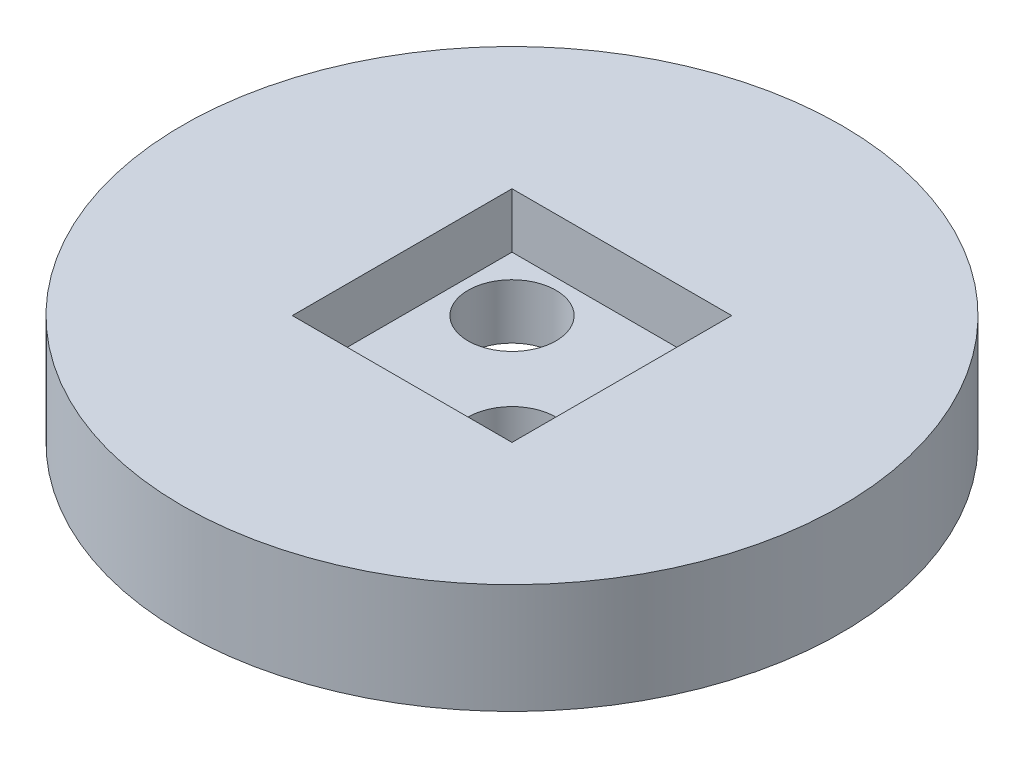
SolidWorks part; units mm, degrees
ref_plane "Front Plane" through (0, 0, 0) normal (0, 0, 1) x (1, 0, 0)
ref_plane "Top Plane" through (0, 0, 0) normal (0, 1, 0) x (1, 0, 0)
ref_plane "Right Plane" through (0, 0, 0) normal (1, 0, 0) x (0, 0, -1)
sketch "Sketch1" plane through (0, 0, 0) normal (0, 1, 0) x (1, 0, 0)
  line L0 (0, 15) -> (11.9476, 15) construction
  line L1 (5, -5) -> (-5, -5)
  line L2 (5, -5) -> (5, 5)
  line L3 (5, 5) -> (-5, 5)
  line L4 (-5, -5) -> (-5, 5)
  line L5 (5, -5) -> (-5, 5) construction
  line L6 (5, 5) -> (-5, -5) construction
  circle A0 centre (0, 0) radius 15
  dimension "D1" = 30
  dimension "D2" = 10
  dimension "D3" = 10
extrude "Boss-Extrude1" add sketch "Sketch1" along normal blind 5
sketch "Sketch2" plane through (0, 0, -5) normal (0, 0, 1) x (1, 0, 0)
  line L1 (-5, 0) -> (5, 0)
  line L2 (-5, 0) -> (-5, 2.5)
  line L3 (-5, 2.5) -> (5, 2.5)
  line L4 (-5, 0) -> (5, 0)
  line L5 (5, 0) -> (5, 5)
  line L6 (5, 5) -> (-5, 5)
  line L7 (-5, 5) -> (-5, 0)
  line L8 (-5, 0) -> (5, 0)
  line L9 (5, 0) -> (5, 5)
  line L10 (5, 5) -> (-5, 5)
  line L11 (-5, 5) -> (-5, 0)
  line L12 (5, 0) -> (5, 2.5)
  line M7 (-5, 0) -> (5, 0)
  line M8 (5, 0) -> (5, 5)
  line M10 (-5, 5) -> (-5, 0)
  dimension "D2" = 2.5
  dimension "D1" = 0
extrude "Boss-Extrude2" add sketch "Sketch2" along normal blind 10 contours L3 M10 M7 M8
sketch "Sketch3" plane through (0, 2.5, 0) normal (0, 1, 0) x (1, 0, 0)
  line L0 (-5, 5) -> (5, -5) construction
  line L1 (-5, -5) -> (5, -5) construction
  line L2 (-5, 5) -> (5, 5) construction
  circle A0 centre (-2.5, 2.5) radius 2
  circle A1 centre (2.5, -2.5) radius 2
  dimension "D1" = 4
  dimension "D2" = 4
  dimension "D3" = 2.5
  dimension "D4" = 2.5
extrude "Cut-Extrude1" cut sketch "Sketch3" against normal blind 10
